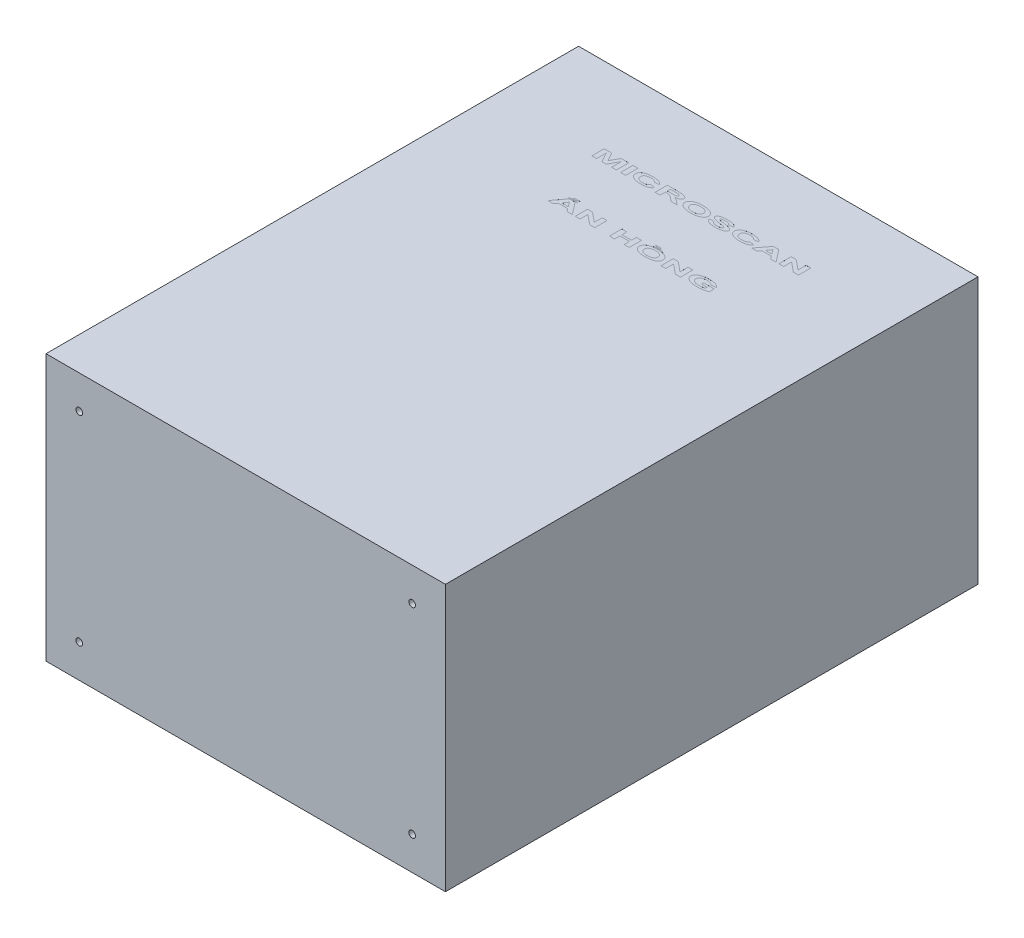
SolidWorks part; units mm, degrees
ref_plane "Front Plane" through (0, 0, 0) normal (0, 0, 1) x (1, 0, 0)
ref_plane "Top Plane" through (0, 0, 0) normal (0, 1, 0) x (1, 0, 0)
ref_plane "Right Plane" through (0, 0, 0) normal (1, 0, 0) x (0, 0, -1)
sketch "Sketch1" plane through (0, 0, 0) normal (0, 0, 1) x (1, 0, 0)
  line L1 (300, -200) -> (-300, -200)
  line L2 (300, -200) -> (300, 200)
  line L3 (300, 200) -> (-300, 200)
  line L4 (-300, -200) -> (-300, 200)
  line L5 (300, -200) -> (-300, 200) construction
  line L6 (300, 200) -> (-300, -200) construction
  point P0 (0, 0)
  dimension "D1" = 400
  dimension "D2" = 600
extrude "Boss-Extrude1" add sketch "Sketch1" along normal blind 800
sketch "Sketch2" plane through (0, 200, 0) normal (0, 1, 0) x (1, 0, 0)
  text T0 "<b>MICROSCAN</b>\r\n\r\n\r\n<b>  ẤN HỒNG</b>" font "Arial" height in points 72
extrude "Cut-Extrude1" cut sketch "Sketch2" against normal blind 0.01
sketch "Sketch3" plane through (0, 0, 800) normal (0, 0, 1) x (1, 0, 0)
  line L0 (0, 0) -> (0, 200) construction
  line L1 (0, 0) -> (300, 0) construction
  line L2 (300, -200) -> (300, 200) construction
  line L3 (300, 200) -> (-300, 200) construction
  circle A0 centre (-250, 150) radius 5
  circle A1 centre (250, 150) radius 5
  circle A2 centre (250, -150) radius 5
  circle A3 centre (-250, -150) radius 5
  dimension "D1" = 300
  dimension "D2" = 500
  dimension "D3" = 10
extrude "Cut-Extrude2" cut sketch "Sketch3" against normal blind 20
